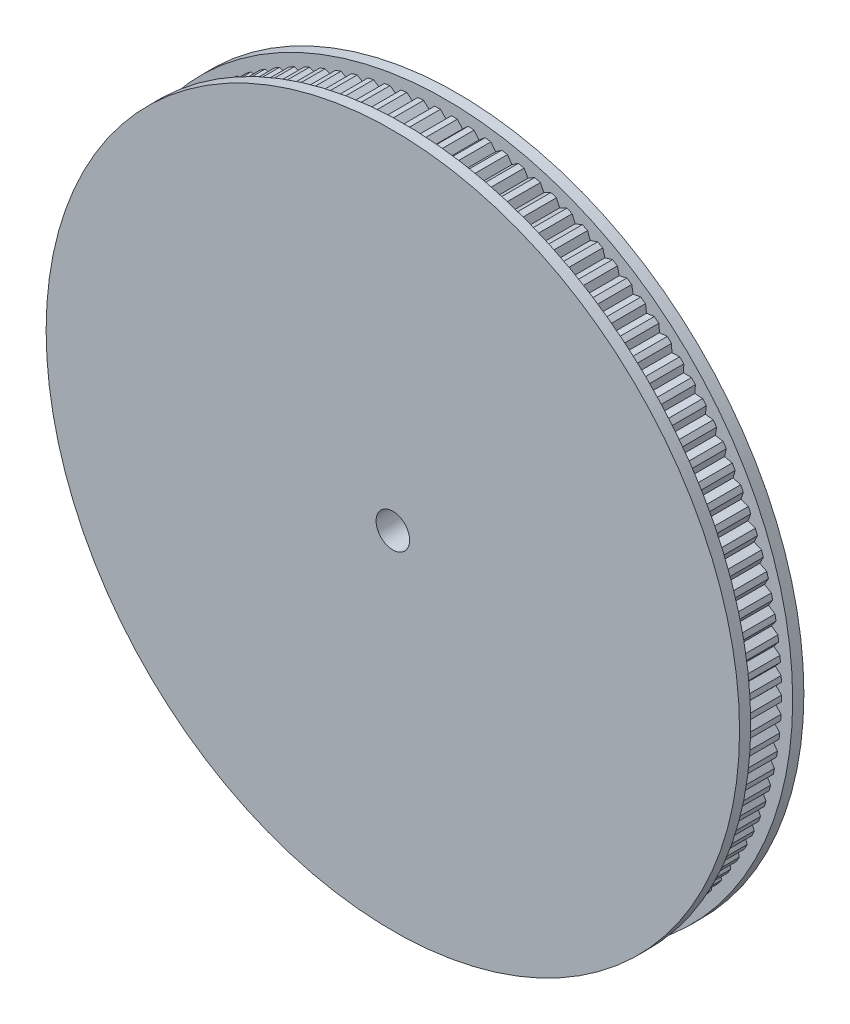
SolidWorks part; units mm, degrees
ref_plane "Front Plane" through (0, 0, 0) normal (0, 0, 1) x (1, 0, 0)
ref_plane "Top Plane" through (0, 0, 0) normal (0, 1, 0) x (1, 0, 0)
ref_plane "Right Plane" through (0, 0, 0) normal (1, 0, 0) x (0, 0, -1)
sketch "Sketch1" plane through (0, 0, 0) normal (0, 0, 1) x (1, 0, 0)
  circle A0 centre (0, 0) radius 60
  circle A1 centre (0, 0) radius 3
  dimension "D1" = 120
extrude "Boss-Extrude1" add sketch "Sketch1" along normal blind 7.5
sketch "Sketch2" plane through (0, 0, 7.5) normal (0, 0, 1) x (1, 0, 0)
  line L0 (0, 60) -> (0, 58) construction
  line L1 (0, -4.125) -> (0, 4.125) construction
  line L2 (0, 59) -> (1.5636, 60.5636)
  line L3 (0, 59) -> (-1.5636, 60.5636)
  line L4 (-1.5636, 60.5636) -> (1.5636, 60.5636)
  line L5 (1.4814, 60.5656) -> (4.6046, 60.4085)
  line L6 (2.9644, 58.9255) -> (4.6046, 60.4085)
  line L7 (2.9644, 58.9255) -> (1.4814, 60.5656)
  line L8 (4.5226, 60.4147) -> (7.6339, 60.1009)
  line L9 (5.9213, 58.7021) -> (7.6339, 60.1009)
  line L10 (5.9213, 58.7021) -> (4.5226, 60.4147)
  line L11 (7.5524, 60.1112) -> (10.644, 59.6414)
  line L12 (8.8633, 58.3305) -> (10.644, 59.6414)
  line L13 (8.8633, 58.3305) -> (7.5524, 60.1112)
  line L14 (10.5631, 59.6558) -> (13.6272, 59.0313)
  line L15 (11.7829, 57.8114) -> (13.6272, 59.0313)
  line L16 (11.7829, 57.8114) -> (10.5631, 59.6558)
  line L17 (13.5471, 59.0497) -> (16.576, 58.272)
  line L18 (14.6727, 57.1464) -> (16.576, 58.272)
  line L19 (14.6727, 57.1464) -> (13.5471, 59.0497)
  line L20 (16.4969, 58.2945) -> (19.4829, 57.3656)
  line L21 (17.5255, 56.337) -> (19.4829, 57.3656)
  line L22 (17.5255, 56.337) -> (16.4969, 58.2945)
  line L23 (19.405, 57.3919) -> (22.3406, 56.3142)
  line L24 (20.3339, 55.3853) -> (22.3406, 56.3142)
  line L25 (20.3339, 55.3853) -> (19.405, 57.3919)
  line L26 (22.2641, 56.3445) -> (25.1418, 55.1206)
  line L27 (23.091, 54.2937) -> (25.1418, 55.1206)
  line L28 (23.091, 54.2937) -> (22.2641, 56.3445)
  line L29 (25.067, 55.1547) -> (27.8796, 53.7877)
  line L30 (25.7898, 53.0649) -> (27.8796, 53.7877)
  line L31 (25.7898, 53.0649) -> (25.067, 55.1547)
  line L32 (27.8066, 53.8255) -> (30.5469, 52.319)
  line L33 (28.4235, 51.7021) -> (30.5469, 52.319)
  line L34 (28.4235, 51.7021) -> (27.8066, 53.8255)
  line L35 (30.4759, 52.3604) -> (33.137, 50.7181)
  line L36 (30.9853, 50.2087) -> (33.137, 50.7181)
  line L37 (30.9853, 50.2087) -> (30.4759, 52.3604)
  line L38 (33.0682, 50.763) -> (35.6435, 48.9891)
  line L39 (33.4689, 48.5884) -> (35.6435, 48.9891)
  line L40 (33.4689, 48.5884) -> (33.0682, 50.763)
  line L41 (35.577, 49.0374) -> (38.0599, 47.1364)
  line L42 (35.8679, 46.8454) -> (38.0599, 47.1364)
  line L43 (35.8679, 46.8454) -> (35.577, 49.0374)
  line L44 (37.9959, 47.188) -> (40.3802, 45.1645)
  line L45 (38.1763, 44.9841) -> (40.3802, 45.1645)
  line L46 (38.1763, 44.9841) -> (37.9959, 47.188)
  line L47 (40.3188, 45.2193) -> (42.5984, 43.0786)
  line L48 (40.3883, 43.0091) -> (42.5984, 43.0786)
  line L49 (40.3883, 43.0091) -> (40.3188, 45.2193)
  line L50 (42.5399, 43.1364) -> (44.7091, 40.8839)
  line L51 (42.4982, 40.9255) -> (44.7091, 40.8839)
  line L52 (42.4982, 40.9255) -> (42.5399, 43.1364)
  line L53 (44.6535, 40.9445) -> (46.7068, 38.5859)
  line L54 (44.5008, 38.7386) -> (46.7068, 38.5859)
  line L55 (44.5008, 38.7386) -> (44.6535, 40.9445)
  line L56 (46.6544, 38.6492) -> (48.5865, 36.1904)
  line L57 (46.391, 36.4537) -> (48.5865, 36.1904)
  line L58 (46.391, 36.4537) -> (46.6544, 38.6492)
  line L59 (48.5373, 36.2563) -> (50.3435, 33.7035)
  line L60 (48.164, 34.0768) -> (50.3435, 33.7035)
  line L61 (48.164, 34.0768) -> (48.5373, 36.2563)
  line L62 (50.2977, 33.7717) -> (51.9733, 31.1314)
  line L63 (49.8153, 31.6138) -> (51.9733, 31.1314)
  line L64 (49.8153, 31.6138) -> (50.2977, 33.7717)
  line L65 (51.931, 31.2019) -> (53.4718, 28.4807)
  line L66 (51.3408, 29.0709) -> (53.4718, 28.4807)
  line L67 (51.3408, 29.0709) -> (51.931, 31.2019)
  line L68 (53.4331, 28.5533) -> (54.8353, 25.7581)
  line L69 (52.7366, 26.4546) -> (54.8353, 25.7581)
  line L70 (52.7366, 26.4546) -> (53.4331, 28.5533)
  line L71 (54.8003, 25.8325) -> (56.0602, 22.9704)
  line L72 (53.9992, 23.7715) -> (56.0602, 22.9704)
  line L73 (53.9992, 23.7715) -> (54.8003, 25.8325)
  line L74 (56.029, 23.0465) -> (57.1436, 20.1247)
  line L75 (55.1254, 21.0283) -> (57.1436, 20.1247)
  line L76 (55.1254, 21.0283) -> (56.029, 23.0465)
  line L77 (57.1162, 20.2022) -> (58.0825, 17.2281)
  line L78 (56.1123, 18.232) -> (58.0825, 17.2281)
  line L79 (56.1123, 18.232) -> (57.1162, 20.2022)
  line L80 (58.0591, 17.3069) -> (58.8748, 14.2881)
  line L81 (56.9575, 15.3896) -> (58.8748, 14.2881)
  line L82 (56.9575, 15.3896) -> (58.0591, 17.3069)
  line L83 (58.8554, 14.3679) -> (59.5183, 11.3119)
  line L84 (57.6588, 12.5084) -> (59.5183, 11.3119)
  line L85 (57.6588, 12.5084) -> (58.8554, 14.3679)
  line L86 (59.5029, 11.3926) -> (60.0115, 8.3071)
  line L87 (58.2145, 9.5956) -> (60.0115, 8.3071)
  line L88 (58.2145, 9.5956) -> (59.5029, 11.3926)
  line L89 (60.0002, 8.3886) -> (60.3531, 5.2814)
  line L90 (58.6231, 6.6585) -> (60.3531, 5.2814)
  line L91 (58.6231, 6.6585) -> (60.0002, 8.3886)
  line L92 (60.3459, 5.3633) -> (60.5422, 2.2423)
  line L93 (58.8836, 3.7046) -> (60.5422, 2.2423)
  line L94 (58.8836, 3.7046) -> (60.3459, 5.3633)
  line L95 (60.5391, 2.3245) -> (60.5784, -0.8024)
  line L96 (58.9953, 0.7414) -> (60.5784, -0.8024)
  line L97 (58.9953, 0.7414) -> (60.5391, 2.3245)
  line L98 (60.5795, -0.7202) -> (60.4616, -3.8451)
  line L99 (58.9581, -2.2237) -> (60.4616, -3.8451)
  line L100 (58.9581, -2.2237) -> (60.5795, -0.7202)
  line L101 (60.4668, -3.7631) -> (60.192, -6.8781)
  line L102 (58.7719, -5.1832) -> (60.192, -6.8781)
  line L103 (58.7719, -5.1832) -> (60.4668, -3.7631)
  line L104 (60.2013, -6.7964) -> (59.7704, -9.8937)
  line L105 (58.4372, -8.1296) -> (59.7704, -9.8937)
  line L106 (58.4372, -8.1296) -> (60.2013, -6.7964)
  line L107 (59.7838, -9.8126) -> (59.1978, -12.8844)
  line L108 (57.9549, -11.0555) -> (59.1978, -12.8844)
  line L109 (57.9549, -11.0555) -> (59.7838, -9.8126)
  line L110 (59.2153, -12.804) -> (58.4757, -15.8424)
  line L111 (57.3263, -13.9534) -> (58.4757, -15.8424)
  line L112 (57.3263, -13.9534) -> (59.2153, -12.804)
  line L113 (58.4971, -15.7631) -> (57.6059, -18.7605)
  line L114 (56.5528, -16.8161) -> (57.6059, -18.7605)
  line L115 (56.5528, -16.8161) -> (58.4971, -15.7631)
  line L116 (57.6313, -18.6823) -> (56.5905, -21.6312)
  line L117 (55.6364, -19.6364) -> (56.5905, -21.6312)
  line L118 (55.6364, -19.6364) -> (57.6313, -18.6823)
  line L119 (56.6198, -21.5544) -> (55.4322, -24.4472)
  line L120 (54.5796, -22.407) -> (55.4322, -24.4472)
  line L121 (54.5796, -22.407) -> (56.6198, -21.5544)
  line L122 (55.4653, -24.372) -> (54.1338, -27.2015)
  line L123 (53.3848, -25.121) -> (54.1338, -27.2015)
  line L124 (53.3848, -25.121) -> (55.4653, -24.372)
  line L125 (54.1707, -27.128) -> (52.6987, -29.887)
  line L126 (52.0552, -27.7715) -> (52.6987, -29.887)
  line L127 (52.0552, -27.7715) -> (54.1707, -27.128)
  line L128 (52.7392, -29.8155) -> (51.1305, -32.4971)
  line L129 (50.5941, -30.3519) -> (51.1305, -32.4971)
  line L130 (50.5941, -30.3519) -> (52.7392, -29.8155)
  line L131 (51.1746, -32.4277) -> (49.4331, -35.0251)
  line L132 (49.0052, -32.8557) -> (49.4331, -35.0251)
  line L133 (49.0052, -32.8557) -> (51.1746, -32.4277)
  line L134 (49.4806, -34.958) -> (47.6109, -37.4646)
  line L135 (47.2925, -35.2764) -> (47.6109, -37.4646)
  line L136 (47.2925, -35.2764) -> (49.4806, -34.958)
  line L137 (47.6617, -37.3999) -> (45.6684, -39.8094)
  line L138 (45.4603, -37.608) -> (45.6684, -39.8094)
  line L139 (45.4603, -37.608) -> (47.6617, -37.3999)
  line L140 (45.7224, -39.7474) -> (43.6105, -42.0537)
  line L141 (43.5133, -39.8446) -> (43.6105, -42.0537)
  line L142 (43.5133, -39.8446) -> (45.7224, -39.7474)
  line L143 (43.6675, -41.9945) -> (41.4425, -44.1918)
  line L144 (41.4563, -41.9806) -> (41.4425, -44.1918)
  line L145 (41.4563, -41.9806) -> (43.6675, -41.9945)
  line L146 (41.5024, -44.1355) -> (39.1697, -46.2182)
  line L147 (39.2947, -44.0105) -> (39.1697, -46.2182)
  line L148 (39.2947, -44.0105) -> (41.5024, -44.1355)
  line L149 (39.2324, -46.165) -> (36.798, -48.1279)
  line L150 (37.0338, -45.9293) -> (36.798, -48.1279)
  line L151 (37.0338, -45.9293) -> (39.2324, -46.165)
  line L152 (36.8633, -48.0779) -> (34.3334, -49.916)
  line L153 (34.6793, -47.732) -> (34.3334, -49.916)
  line L154 (34.6793, -47.732) -> (36.8633, -48.0779)
  line L155 (34.4011, -49.8694) -> (31.7821, -51.578)
  line L156 (32.2373, -49.4142) -> (31.7821, -51.578)
  line L157 (32.2373, -49.4142) -> (34.4011, -49.8694)
  line L158 (31.852, -51.5348) -> (29.1504, -53.1097)
  line L159 (29.7138, -50.9715) -> (29.1504, -53.1097)
  line L160 (29.7138, -50.9715) -> (31.852, -51.5348)
  line L161 (29.2225, -53.0701) -> (26.4451, -54.5073)
  line L162 (27.1152, -52.4001) -> (26.4451, -54.5073)
  line L163 (27.1152, -52.4001) -> (29.2225, -53.0701)
  line L164 (26.5191, -54.4714) -> (23.6731, -55.7672)
  line L165 (24.4482, -53.6963) -> (23.6731, -55.7672)
  line L166 (24.4482, -53.6963) -> (26.5191, -54.4714)
  line L167 (23.7487, -55.735) -> (20.8412, -56.8862)
  line L168 (21.7193, -54.8568) -> (20.8412, -56.8862)
  line L169 (21.7193, -54.8568) -> (23.7487, -55.735)
  line L170 (20.9183, -56.8578) -> (17.9566, -57.8615)
  line L171 (18.9357, -55.8788) -> (17.9566, -57.8615)
  line L172 (18.9357, -55.8788) -> (20.9183, -56.8578)
  line L173 (18.0351, -57.8371) -> (15.0267, -58.6906)
  line L174 (16.1042, -56.7596) -> (15.0267, -58.6906)
  line L175 (16.1042, -56.7596) -> (18.0351, -57.8371)
  line L176 (15.1064, -58.6702) -> (12.0589, -59.3715)
  line L177 (13.232, -57.4971) -> (12.0589, -59.3715)
  line L178 (13.232, -57.4971) -> (15.1064, -58.6702)
  line L179 (12.1395, -59.3551) -> (9.0606, -59.9024)
  line L180 (10.3264, -58.0893) -> (9.0606, -59.9024)
  line L181 (10.3264, -58.0893) -> (12.1395, -59.3551)
  line L182 (9.1419, -59.89) -> (6.0394, -60.282)
  line L183 (7.3947, -58.5348) -> (6.0394, -60.282)
  line L184 (7.3947, -58.5348) -> (9.1419, -59.89)
  line L185 (6.1212, -60.2737) -> (3.0029, -60.5093)
  line L186 (4.4443, -58.8324) -> (3.0029, -60.5093)
  line L187 (4.4443, -58.8324) -> (6.1212, -60.2737)
  line L188 (3.085, -60.5052) -> (-0.0411, -60.5837)
  line L189 (1.4827, -58.9814) -> (-0.0411, -60.5837)
  line L190 (1.4827, -58.9814) -> (3.085, -60.5052)
  line L191 (0.0411, -60.5837) -> (-3.085, -60.5052)
  line L192 (-1.4827, -58.9814) -> (-3.085, -60.5052)
  line L193 (-1.4827, -58.9814) -> (0.0411, -60.5837)
  line L194 (-3.0029, -60.5093) -> (-6.1212, -60.2737)
  line L195 (-4.4443, -58.8324) -> (-6.1212, -60.2737)
  line L196 (-4.4443, -58.8324) -> (-3.0029, -60.5093)
  line L197 (-6.0394, -60.282) -> (-9.1419, -59.89)
  line L198 (-7.3947, -58.5348) -> (-9.1419, -59.89)
  line L199 (-7.3947, -58.5348) -> (-6.0394, -60.282)
  line L200 (-9.0606, -59.9024) -> (-12.1395, -59.3551)
  line L201 (-10.3264, -58.0893) -> (-12.1395, -59.3551)
  line L202 (-10.3264, -58.0893) -> (-9.0606, -59.9024)
  line L203 (-12.0589, -59.3715) -> (-15.1064, -58.6702)
  line L204 (-13.232, -57.4971) -> (-15.1064, -58.6702)
  line L205 (-13.232, -57.4971) -> (-12.0589, -59.3715)
  line L206 (-15.0267, -58.6906) -> (-18.0351, -57.8371)
  line L207 (-16.1042, -56.7596) -> (-18.0351, -57.8371)
  line L208 (-16.1042, -56.7596) -> (-15.0267, -58.6906)
  line L209 (-17.9566, -57.8615) -> (-20.9183, -56.8578)
  line L210 (-18.9357, -55.8788) -> (-20.9183, -56.8578)
  line L211 (-18.9357, -55.8788) -> (-17.9566, -57.8615)
  line L212 (-20.8412, -56.8862) -> (-23.7487, -55.735)
  line L213 (-21.7193, -54.8568) -> (-23.7487, -55.735)
  line L214 (-21.7193, -54.8568) -> (-20.8412, -56.8862)
  line L215 (-23.6731, -55.7672) -> (-26.5191, -54.4714)
  line L216 (-24.4482, -53.6963) -> (-26.5191, -54.4714)
  line L217 (-24.4482, -53.6963) -> (-23.6731, -55.7672)
  line L218 (-26.4451, -54.5073) -> (-29.2225, -53.0701)
  line L219 (-27.1152, -52.4001) -> (-29.2225, -53.0701)
  line L220 (-27.1152, -52.4001) -> (-26.4451, -54.5073)
  line L221 (-29.1504, -53.1097) -> (-31.852, -51.5348)
  line L222 (-29.7138, -50.9715) -> (-31.852, -51.5348)
  line L223 (-29.7138, -50.9715) -> (-29.1504, -53.1097)
  line L224 (-31.7821, -51.578) -> (-34.4011, -49.8694)
  line L225 (-32.2373, -49.4142) -> (-34.4011, -49.8694)
  line L226 (-32.2373, -49.4142) -> (-31.7821, -51.578)
  line L227 (-34.3334, -49.916) -> (-36.8633, -48.0779)
  line L228 (-34.6793, -47.732) -> (-36.8633, -48.0779)
  line L229 (-34.6793, -47.732) -> (-34.3334, -49.916)
  line L230 (-36.798, -48.1279) -> (-39.2324, -46.165)
  line L231 (-37.0338, -45.9293) -> (-39.2324, -46.165)
  line L232 (-37.0338, -45.9293) -> (-36.798, -48.1279)
  line L233 (-39.1697, -46.2182) -> (-41.5024, -44.1355)
  line L234 (-39.2947, -44.0105) -> (-41.5024, -44.1355)
  line L235 (-39.2947, -44.0105) -> (-39.1697, -46.2182)
  line L236 (-41.4425, -44.1918) -> (-43.6675, -41.9945)
  line L237 (-41.4563, -41.9806) -> (-43.6675, -41.9945)
  line L238 (-41.4563, -41.9806) -> (-41.4425, -44.1918)
  line L239 (-43.6105, -42.0537) -> (-45.7224, -39.7474)
  line L240 (-43.5133, -39.8446) -> (-45.7224, -39.7474)
  line L241 (-43.5133, -39.8446) -> (-43.6105, -42.0537)
  line L242 (-45.6684, -39.8094) -> (-47.6617, -37.3999)
  line L243 (-45.4603, -37.608) -> (-47.6617, -37.3999)
  line L244 (-45.4603, -37.608) -> (-45.6684, -39.8094)
  line L245 (-47.6109, -37.4646) -> (-49.4806, -34.958)
  line L246 (-47.2925, -35.2764) -> (-49.4806, -34.958)
  line L247 (-47.2925, -35.2764) -> (-47.6109, -37.4646)
  line L248 (-49.4331, -35.0251) -> (-51.1746, -32.4277)
  line L249 (-49.0052, -32.8557) -> (-51.1746, -32.4277)
  line L250 (-49.0052, -32.8557) -> (-49.4331, -35.0251)
  line L251 (-51.1305, -32.4971) -> (-52.7392, -29.8155)
  line L252 (-50.5941, -30.3519) -> (-52.7392, -29.8155)
  line L253 (-50.5941, -30.3519) -> (-51.1305, -32.4971)
  line L254 (-52.6987, -29.887) -> (-54.1707, -27.128)
  line L255 (-52.0552, -27.7715) -> (-54.1707, -27.128)
  line L256 (-52.0552, -27.7715) -> (-52.6987, -29.887)
  line L257 (-54.1338, -27.2015) -> (-55.4653, -24.372)
  line L258 (-53.3848, -25.121) -> (-55.4653, -24.372)
  line L259 (-53.3848, -25.121) -> (-54.1338, -27.2015)
  line L260 (-55.4322, -24.4472) -> (-56.6198, -21.5544)
  line L261 (-54.5796, -22.407) -> (-56.6198, -21.5544)
  line L262 (-54.5796, -22.407) -> (-55.4322, -24.4472)
  line L263 (-56.5905, -21.6312) -> (-57.6313, -18.6823)
  line L264 (-55.6364, -19.6364) -> (-57.6313, -18.6823)
  line L265 (-55.6364, -19.6364) -> (-56.5905, -21.6312)
  line L266 (-57.6059, -18.7605) -> (-58.4971, -15.7631)
  line L267 (-56.5528, -16.8161) -> (-58.4971, -15.7631)
  line L268 (-56.5528, -16.8161) -> (-57.6059, -18.7605)
  line L269 (-58.4757, -15.8424) -> (-59.2153, -12.804)
  line L270 (-57.3263, -13.9534) -> (-59.2153, -12.804)
  line L271 (-57.3263, -13.9534) -> (-58.4757, -15.8424)
  line L272 (-59.1978, -12.8844) -> (-59.7838, -9.8126)
  line L273 (-57.9549, -11.0555) -> (-59.7838, -9.8126)
  line L274 (-57.9549, -11.0555) -> (-59.1978, -12.8844)
  line L275 (-59.7704, -9.8937) -> (-60.2013, -6.7964)
  line L276 (-58.4372, -8.1296) -> (-60.2013, -6.7964)
  line L277 (-58.4372, -8.1296) -> (-59.7704, -9.8937)
  line L278 (-60.192, -6.8781) -> (-60.4668, -3.7631)
  line L279 (-58.7719, -5.1832) -> (-60.4668, -3.7631)
  line L280 (-58.7719, -5.1832) -> (-60.192, -6.8781)
  line L281 (-60.4616, -3.8451) -> (-60.5795, -0.7202)
  line L282 (-58.9581, -2.2237) -> (-60.5795, -0.7202)
  line L283 (-58.9581, -2.2237) -> (-60.4616, -3.8451)
  line L284 (-60.5784, -0.8024) -> (-60.5391, 2.3245)
  line L285 (-58.9953, 0.7414) -> (-60.5391, 2.3245)
  line L286 (-58.9953, 0.7414) -> (-60.5784, -0.8024)
  line L287 (-60.5422, 2.2423) -> (-60.3459, 5.3633)
  line L288 (-58.8836, 3.7046) -> (-60.3459, 5.3633)
  line L289 (-58.8836, 3.7046) -> (-60.5422, 2.2423)
  line L290 (-60.3531, 5.2814) -> (-60.0002, 8.3886)
  line L291 (-58.6231, 6.6585) -> (-60.0002, 8.3886)
  line L292 (-58.6231, 6.6585) -> (-60.3531, 5.2814)
  line L293 (-60.0115, 8.3071) -> (-59.5029, 11.3926)
  line L294 (-58.2145, 9.5956) -> (-59.5029, 11.3926)
  line L295 (-58.2145, 9.5956) -> (-60.0115, 8.3071)
  line L296 (-59.5183, 11.3119) -> (-58.8554, 14.3679)
  line L297 (-57.6588, 12.5084) -> (-58.8554, 14.3679)
  line L298 (-57.6588, 12.5084) -> (-59.5183, 11.3119)
  line L299 (-58.8748, 14.2881) -> (-58.0591, 17.3069)
  line L300 (-56.9575, 15.3896) -> (-58.0591, 17.3069)
  line L301 (-56.9575, 15.3896) -> (-58.8748, 14.2881)
  line L302 (-58.0825, 17.2281) -> (-57.1162, 20.2022)
  line L303 (-56.1123, 18.232) -> (-57.1162, 20.2022)
  line L304 (-56.1123, 18.232) -> (-58.0825, 17.2281)
  line L305 (-57.1436, 20.1247) -> (-56.029, 23.0465)
  line L306 (-55.1254, 21.0283) -> (-56.029, 23.0465)
  line L307 (-55.1254, 21.0283) -> (-57.1436, 20.1247)
  line L308 (-56.0602, 22.9704) -> (-54.8003, 25.8325)
  line L309 (-53.9992, 23.7715) -> (-54.8003, 25.8325)
  line L310 (-53.9992, 23.7715) -> (-56.0602, 22.9704)
  line L311 (-54.8353, 25.7581) -> (-53.4331, 28.5533)
  line L312 (-52.7366, 26.4546) -> (-53.4331, 28.5533)
  line L313 (-52.7366, 26.4546) -> (-54.8353, 25.7581)
  line L314 (-53.4718, 28.4807) -> (-51.931, 31.2019)
  line L315 (-51.3408, 29.0709) -> (-51.931, 31.2019)
  line L316 (-51.3408, 29.0709) -> (-53.4718, 28.4807)
  line L317 (-51.9733, 31.1314) -> (-50.2977, 33.7717)
  line L318 (-49.8153, 31.6138) -> (-50.2977, 33.7717)
  line L319 (-49.8153, 31.6138) -> (-51.9733, 31.1314)
  line L320 (-50.3435, 33.7035) -> (-48.5373, 36.2563)
  line L321 (-48.164, 34.0768) -> (-48.5373, 36.2563)
  line L322 (-48.164, 34.0768) -> (-50.3435, 33.7035)
  line L323 (-48.5865, 36.1904) -> (-46.6544, 38.6492)
  line L324 (-46.391, 36.4537) -> (-46.6544, 38.6492)
  line L325 (-46.391, 36.4537) -> (-48.5865, 36.1904)
  line L326 (-46.7068, 38.5859) -> (-44.6535, 40.9445)
  line L327 (-44.5008, 38.7386) -> (-44.6535, 40.9445)
  line L328 (-44.5008, 38.7386) -> (-46.7068, 38.5859)
  line L329 (-44.7091, 40.8839) -> (-42.5399, 43.1364)
  line L330 (-42.4982, 40.9255) -> (-42.5399, 43.1364)
  line L331 (-42.4982, 40.9255) -> (-44.7091, 40.8839)
  line L332 (-42.5984, 43.0786) -> (-40.3188, 45.2193)
  line L333 (-40.3883, 43.0091) -> (-40.3188, 45.2193)
  line L334 (-40.3883, 43.0091) -> (-42.5984, 43.0786)
  line L335 (-40.3802, 45.1645) -> (-37.9959, 47.188)
  line L336 (-38.1763, 44.9841) -> (-37.9959, 47.188)
  line L337 (-38.1763, 44.9841) -> (-40.3802, 45.1645)
  line L338 (-38.0599, 47.1364) -> (-35.577, 49.0374)
  line L339 (-35.8679, 46.8454) -> (-35.577, 49.0374)
  line L340 (-35.8679, 46.8454) -> (-38.0599, 47.1364)
  line L341 (-35.6435, 48.9891) -> (-33.0682, 50.763)
  line L342 (-33.4689, 48.5884) -> (-33.0682, 50.763)
  line L343 (-33.4689, 48.5884) -> (-35.6435, 48.9891)
  line L344 (-33.137, 50.7181) -> (-30.4759, 52.3604)
  line L345 (-30.9853, 50.2087) -> (-30.4759, 52.3604)
  line L346 (-30.9853, 50.2087) -> (-33.137, 50.7181)
  line L347 (-30.5469, 52.319) -> (-27.8066, 53.8255)
  line L348 (-28.4235, 51.7021) -> (-27.8066, 53.8255)
  line L349 (-28.4235, 51.7021) -> (-30.5469, 52.319)
  line L350 (-27.8796, 53.7877) -> (-25.067, 55.1547)
  line L351 (-25.7898, 53.0649) -> (-25.067, 55.1547)
  line L352 (-25.7898, 53.0649) -> (-27.8796, 53.7877)
  line L353 (-25.1418, 55.1206) -> (-22.2641, 56.3445)
  line L354 (-23.091, 54.2937) -> (-22.2641, 56.3445)
  line L355 (-23.091, 54.2937) -> (-25.1418, 55.1206)
  line L356 (-22.3406, 56.3142) -> (-19.405, 57.3919)
  line L357 (-20.3339, 55.3853) -> (-19.405, 57.3919)
  line L358 (-20.3339, 55.3853) -> (-22.3406, 56.3142)
  line L359 (-19.4829, 57.3656) -> (-16.4969, 58.2945)
  line L360 (-17.5255, 56.337) -> (-16.4969, 58.2945)
  line L361 (-17.5255, 56.337) -> (-19.4829, 57.3656)
  line L362 (-16.576, 58.272) -> (-13.5471, 59.0497)
  line L363 (-14.6727, 57.1464) -> (-13.5471, 59.0497)
  line L364 (-14.6727, 57.1464) -> (-16.576, 58.272)
  line L365 (-13.6272, 59.0313) -> (-10.5631, 59.6558)
  line L366 (-11.7829, 57.8114) -> (-10.5631, 59.6558)
  line L367 (-11.7829, 57.8114) -> (-13.6272, 59.0313)
  line L368 (-10.644, 59.6414) -> (-7.5524, 60.1112)
  line L369 (-8.8633, 58.3305) -> (-7.5524, 60.1112)
  line L370 (-8.8633, 58.3305) -> (-10.644, 59.6414)
  line L371 (-7.6339, 60.1009) -> (-4.5226, 60.4147)
  line L372 (-5.9213, 58.7021) -> (-4.5226, 60.4147)
  line L373 (-5.9213, 58.7021) -> (-7.6339, 60.1009)
  line L374 (-4.6046, 60.4085) -> (-1.4814, 60.5656)
  line L375 (-2.9644, 58.9255) -> (-1.4814, 60.5656)
  line L376 (-2.9644, 58.9255) -> (-4.6046, 60.4085)
  circle A0 centre (0, 0) radius 60 construction
  point P384 (0, 0)
  dimension "D1" = 125
extrude "Cut-Extrude1" cut sketch "Sketch2" against normal blind 7.5
sketch "Sketch3" plane through (0, 0, 7.5) normal (0, 0, 1) x (1, 0, 0)
  circle A0 centre (0, 0) radius 62
  circle A1 centre (0, 0) radius 3
extrude "Boss-Extrude2" add sketch "Sketch3" along normal blind 2 contours A0 A1
sketch "Sketch4" plane through (0, 0, 0) normal (0, 0, -1) x (-1, 0, 0)
  circle A0 centre (0, 0) radius 62
  circle A1 centre (0, 0) radius 3
extrude "Boss-Extrude3" add sketch "Sketch4" along normal blind 2
